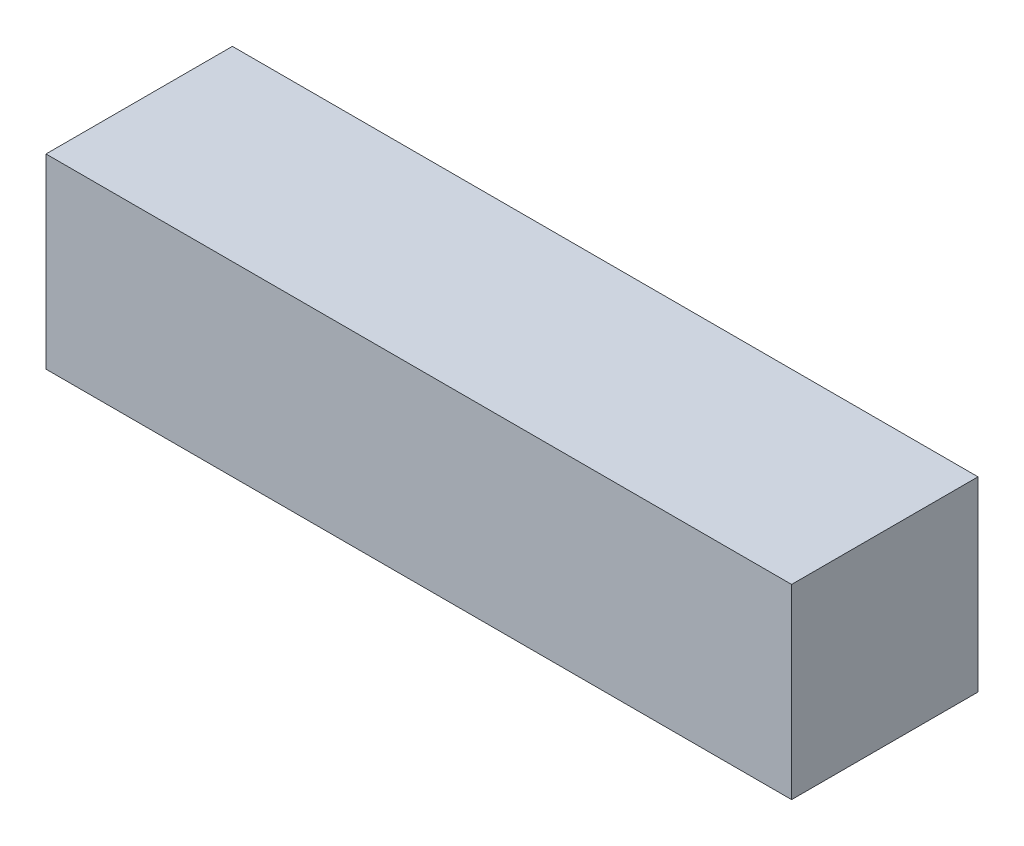
SolidWorks part; units mm, degrees
ref_plane "Front Plane" through (0, 0, 0) normal (0, 0, 1) x (1, 0, 0)
ref_plane "Top Plane" through (0, 0, 0) normal (0, 1, 0) x (1, 0, 0)
ref_plane "Right Plane" through (0, 0, 0) normal (1, 0, 0) x (0, 0, -1)
sketch "Sketch1" plane through (0, 0, 0) normal (0, 1, 0) x (1, 0, 0)
  line L0 (-20, 5) -> (20, -5) construction
  line L1 (-20, 5) -> (20, 5)
  line L2 (-20, 5) -> (-20, -5)
  line L3 (-20, -5) -> (20, -5)
  line L4 (20, 5) -> (20, -5)
  dimension "D1" = 40
  dimension "D2" = 10
extrude "Boss-Extrude1" add sketch "Sketch1" along normal blind 10
